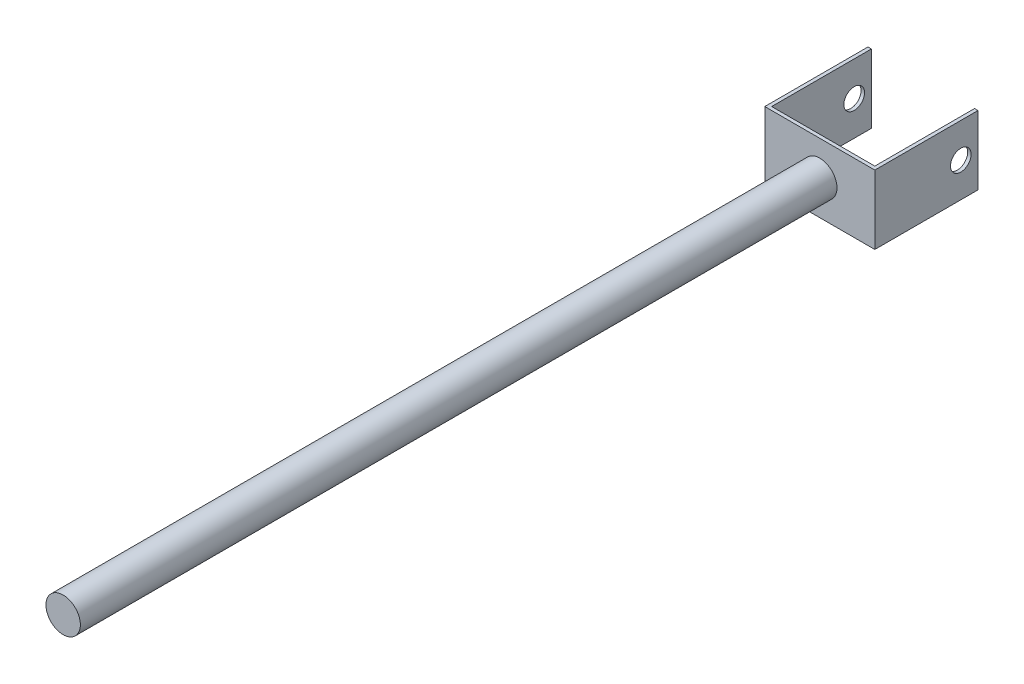
SolidWorks part; units mm, degrees
ref_plane "Front Plane" through (0, 0, 0) normal (0, 0, 1) x (1, 0, 0)
ref_plane "Top Plane" through (0, 0, 0) normal (0, 1, 0) x (1, 0, 0)
ref_plane "Right Plane" through (0, 0, 0) normal (1, 0, 0) x (0, 0, -1)
sketch "Sketch1" plane through (0, 0, 0) normal (0, 1, 0) x (1, 0, 0)
  line L0 (5, 150) -> (5, 5)
  line L1 (0, 0) -> (160, 0)
  line L2 (0, 0) -> (0, 150)
  line L3 (0, 150) -> (5, 150)
  line L4 (160, 0) -> (160, 150)
  line L5 (5, 5) -> (155, 5)
  line L6 (155, 5) -> (155, 150)
  line L7 (155, 150) -> (160, 150)
  dimension "D1" = 160
  dimension "D2" = 150
  dimension "D3" = 5
  dimension "D4" = 5
  dimension "D5" = 5
extrude "Boss-Extrude3" add sketch "Sketch1" along normal mid plane 100
sketch "Sketch4" plane through (0, 0, 0) normal (0, 0, 1) x (1, 0, 0)
  line L0 (80, 50) -> (80, -50) construction
  line L1 (0, 50) -> (160, 50) construction
  line L2 (0, -50) -> (160, -50) construction
  line L3 (0, 0) -> (80, 0) construction
  line L4 (160, 50) -> (160, -50) construction
  circle A0 centre (80, 0) radius 25
  dimension "D1" = 50
  dimension "D2" = 80
extrude "Boss-Extrude4" add sketch "Sketch4" along normal blind 1100
sketch "Sketch5" plane through (160, 0, 0) normal (1, 0, 0) x (0, 0, -1)
  line L0 (0, 0) -> (125, 0) construction
  circle A0 centre (125, 0) radius 15
  dimension "D2" = 30
  dimension "D1" = 125
extrude "Cut-Extrude1" cut sketch "Sketch5" against normal through all
